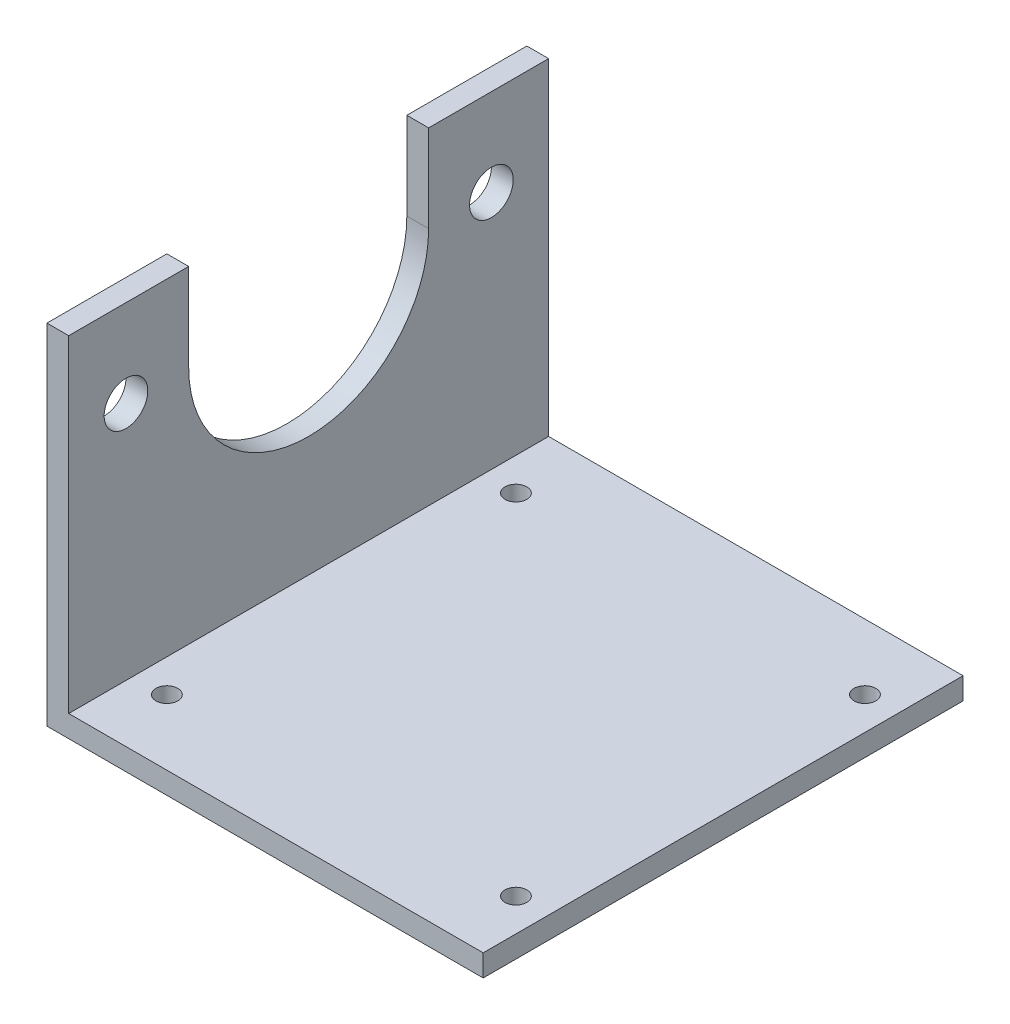
SolidWorks part; units mm, degrees
material "AISI 1020"
ref_plane "Front Plane" through (0, 0, 0) normal (0, 0, 1) x (1, 0, 0)
ref_plane "Top Plane" through (0, 0, 0) normal (0, 1, 0) x (1, 0, 0)
ref_plane "Right Plane" through (0, 0, 0) normal (1, 0, 0) x (0, 0, -1)
sketch "Sketch1" plane through (0, 0, 0) normal (0, 0, 1) x (1, 0, 0)
  line L0 (0, 0) -> (0, 95.25)
  line L1 (0, 95.25) -> (-6.35, 95.25)
  line L2 (-6.35, 95.25) -> (-6.35, -6.35)
  line L3 (-6.35, -6.35) -> (120.65, -6.35)
  line L4 (120.65, -6.35) -> (120.65, 0)
  line L5 (120.65, 0) -> (0, 0)
  dimension "D1" = 6.35
  dimension "D2" = 101.6
  dimension "D3" = 127
extrude "Boss-Extrude1" add sketch "Sketch1" along normal mid plane 139.7
sketch "Sketch2" plane through (0, 0, 0) normal (1, 0, 0) x (0, 0, -1)
  line L0 (-34.925, 69.85) -> (-34.925, 95.25)
  line L1 (-69.85, 95.25) -> (69.85, 95.25) construction
  line L2 (-34.925, 95.25) -> (34.925, 95.25)
  line L3 (34.925, 95.25) -> (34.925, 69.85)
  line L4 (0, 95.25) -> (0, 34.925) construction
  line L5 (-53.1876, 69.85) -> (0, 69.85) construction
  arc A0 (-34.925, 69.85) -> (34.925, 69.85) centre (0, 69.85) ccw
  circle A1 centre (-53.1876, 69.85) radius 6.35
  circle A2 centre (53.1876, 69.85) radius 6.35
  dimension "D1" = 34.925
  dimension "D3" = 12.7
  dimension "D2" = 25.4
  dimension "D4" = 53.1876
extrude "Cut-Extrude1" cut sketch "Sketch2" against normal up to next
sketch "Sketch3" plane through (0, 0, 0) normal (0, 1, 0) x (1, 0, 0)
  line L0 (60.325, 69.85) -> (60.325, 0) construction
  line L1 (60.325, 0) -> (0, 0) construction
  line L3 (111.125, -50.8) -> (9.525, -50.8) construction
  line L4 (120.65, 69.85) -> (0, 69.85)
  line L5 (0, 69.85) -> (0, -69.85)
  line L6 (0, -69.85) -> (120.65, -69.85)
  line L7 (120.65, -69.85) -> (120.65, 69.85)
  line L8 (120.65, 69.85) -> (0, 69.85) construction
  line L9 (0, 69.85) -> (0, -69.85) construction
  line L10 (0, -69.85) -> (120.65, -69.85) construction
  line L11 (120.65, -69.85) -> (120.65, 69.85) construction
  line L12 (111.125, -50.8) -> (111.125, 50.8) construction
  line L13 (111.125, 50.8) -> (9.525, 50.8) construction
  line L14 (9.525, -50.8) -> (9.525, 50.8) construction
  line L15 (111.125, -50.8) -> (9.525, 50.8) construction
  line L16 (111.125, 50.8) -> (9.525, -50.8) construction
  circle A0 centre (9.525, 50.8) radius 3.175
  circle A1 centre (111.125, 50.8) radius 3.175
  circle A2 centre (9.525, -50.8) radius 3.175
  circle A3 centre (111.125, -50.8) radius 3.175
  dimension "D3" = 6.35
  dimension "D2" = 101.6
  dimension "D1" = 0
extrude "Cut-Extrude2" cut sketch "Sketch3" against normal up to next
